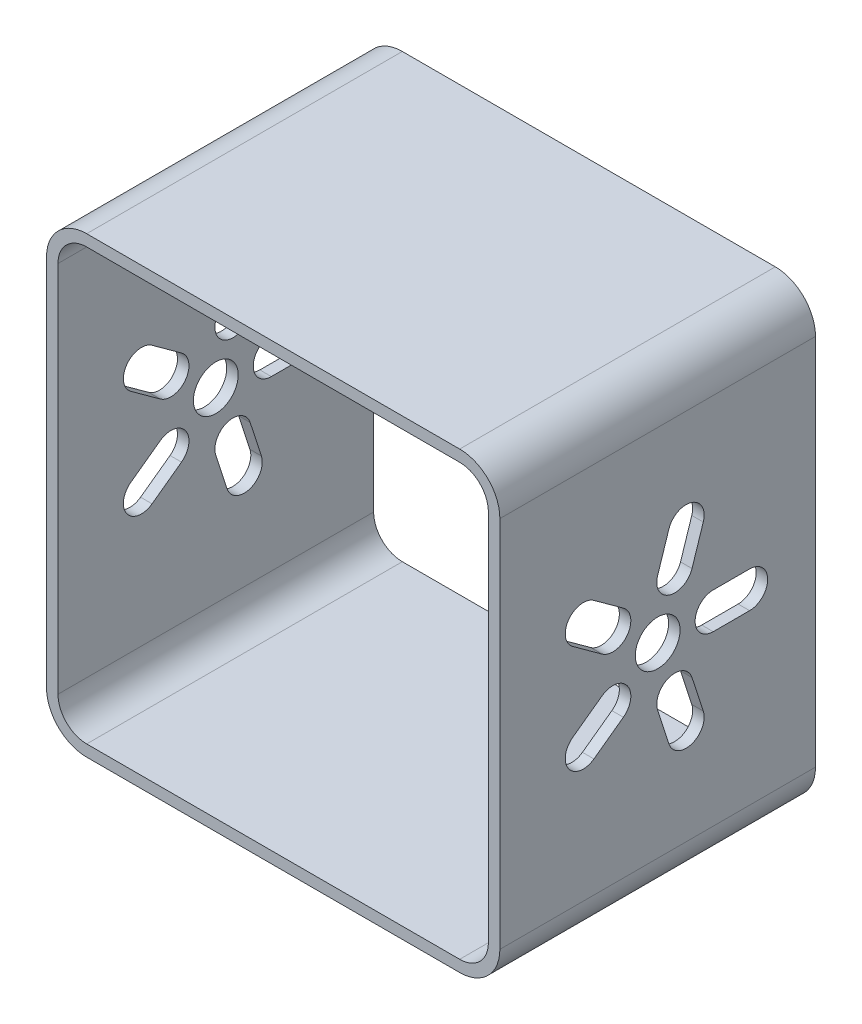
SolidWorks part; units mm, degrees
ref_plane "Plan de face" through (0, 0, 0) normal (0, 0, 1) x (1, 0, 0)
ref_plane "Plan de dessus" through (0, 0, 0) normal (0, 1, 0) x (1, 0, 0)
ref_plane "Plan de droite" through (0, 0, 0) normal (1, 0, 0) x (0, 0, -1)
sketch "Esquisse1" plane through (0, 0, 0) normal (0, 0, 1) x (1, 0, 0)
  line L0 (-79, 65) -> (-79, -65)
  line L2 (-65, 75) -> (65, 75)
  line L3 (-75, 65) -> (-75, -65)
  line L13 (-65, -75) -> (65, -75)
  line L14 (75, 65) -> (75, -65)
  line L15 (-75, 75) -> (75, -75) construction
  line L16 (-75, -75) -> (75, 75) construction
  line L17 (-65, -79) -> (65, -79)
  line L18 (79, 65) -> (79, -65)
  line L19 (-65, 79) -> (65, 79)
  arc A4 (-75, -65) -> (-65, -75) centre (-65, -65) ccw
  arc A5 (65, -75) -> (75, -65) centre (65, -65) ccw
  arc A6 (65, 75) -> (75, 65) centre (65, 65) cw
  arc A7 (-65, 75) -> (-75, 65) centre (-65, 65) ccw
  arc A8 (-79, -65) -> (-65, -79) centre (-65, -65) ccw
  arc A9 (65, -79) -> (79, -65) centre (65, -65) ccw
  arc A10 (65, 79) -> (79, 65) centre (65, 65) cw
  arc A11 (-65, 79) -> (-79, 65) centre (-65, 65) ccw
  point P0 (0, 0)
  dimension "D3" = 10
  dimension "D1" = 150
  dimension "D2" = 150
  dimension "D4" = 4
extrude "Boss.-Extru.1" add sketch "Esquisse1" along normal blind 110
sketch "Esquisse2" plane through (-79, 0, 0) normal (-1, 0, 0) x (0, 0, 1)
  line L0 (55, 65) -> (55, -65) construction
  line L7 (110, 65) -> (0, 65) construction
  line L8 (110, -65) -> (0, -65) construction
  line L9 (22.9641, 0) -> (35.6494, 0) construction
  line L10 (22.9641, 6.2962) -> (35.6494, 6.2962)
  line L11 (22.9641, -6.2962) -> (35.6494, -6.2962)
  line L12 (45.1004, 30.468) -> (49.0203, 18.4035) construction
  line L13 (51.0884, 32.4136) -> (55.0084, 20.3491)
  line L14 (39.1123, 28.5223) -> (43.0323, 16.4579)
  line L15 (80.9176, 18.8302) -> (70.6549, 11.374) construction
  line L16 (84.6184, 13.7365) -> (74.3558, 6.2802)
  line L17 (77.2168, 23.924) -> (66.9541, 16.4677)
  line L18 (80.9176, -18.8302) -> (70.6549, -11.374) construction
  line L19 (77.2168, -23.924) -> (66.9541, -16.4677)
  line L20 (84.6184, -13.7365) -> (74.3558, -6.2802)
  line L21 (45.1004, -30.468) -> (49.0203, -18.4035) construction
  line L22 (39.1123, -28.5223) -> (43.0323, -16.4579)
  line L23 (51.0884, -32.4136) -> (55.0084, -20.3491)
  circle A0 centre (55, 0) radius 7.8091
  arc A1 (22.9641, 6.2962) -> (22.9641, -6.2962) centre (22.9641, 0) ccw
  arc A2 (35.6494, -6.2962) -> (35.6494, 6.2962) centre (35.6494, 0) ccw
  arc A3 (51.0884, 32.4136) -> (39.1123, 28.5223) centre (45.1004, 30.468) ccw
  arc A4 (43.0323, 16.4579) -> (55.0084, 20.3491) centre (49.0203, 18.4035) ccw
  arc A5 (84.6184, 13.7365) -> (77.2168, 23.924) centre (80.9176, 18.8302) ccw
  arc A6 (66.9541, 16.4677) -> (74.3558, 6.2802) centre (70.6549, 11.374) ccw
  arc A7 (77.2168, -23.924) -> (84.6184, -13.7365) centre (80.9176, -18.8302) ccw
  arc A8 (74.3558, -6.2802) -> (66.9541, -16.4677) centre (70.6549, -11.374) ccw
  arc A9 (39.1123, -28.5223) -> (51.0884, -32.4136) centre (45.1004, -30.468) ccw
  arc A10 (55.0084, -20.3491) -> (43.0323, -16.4579) centre (49.0203, -18.4035) ccw
  point P4 (29.3067, 0)
  point P20 (47.0603, 24.4357)
  point P27 (75.7863, 15.1021)
  point P34 (75.7863, -15.1021)
  point P41 (47.0603, -24.4357)
  point P46 (55, 0)
  dimension "D1" = 5
extrude "Enlèv. mat.-Extru.1" cut sketch "Esquisse2" against normal through all
